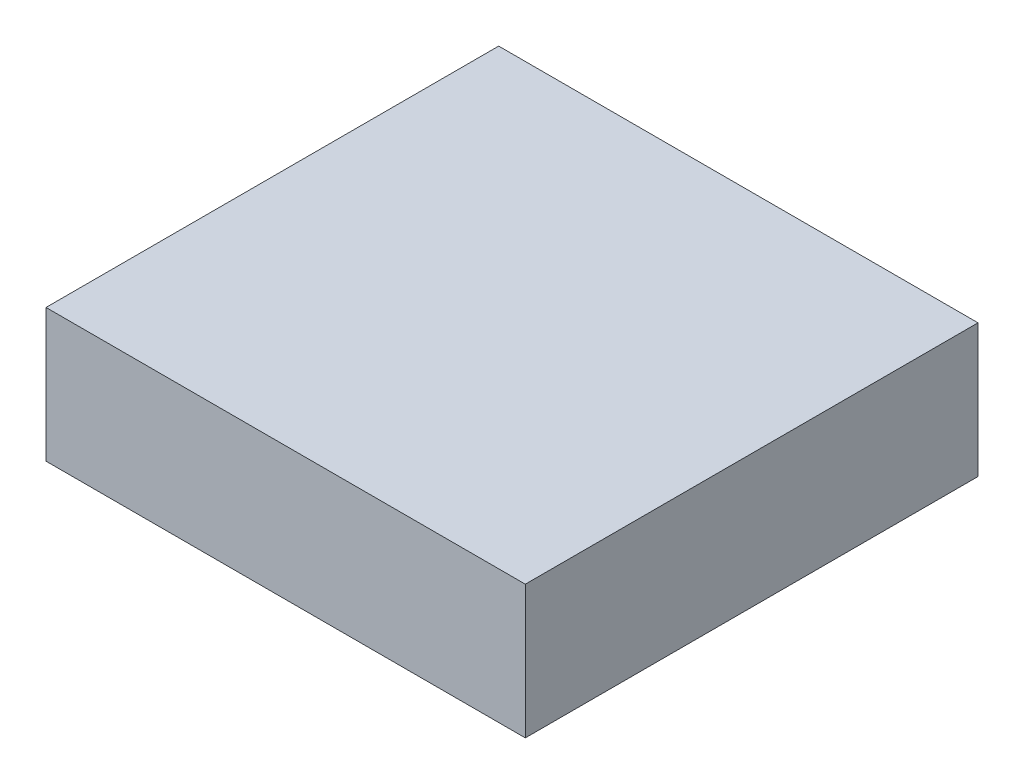
SolidWorks part; units mm, degrees
material "Aço 4140"
ref_plane "Plano frontal" through (0, 0, 0) normal (0, 0, 1) x (1, 0, 0)
ref_plane "Plano superior" through (0, 0, 0) normal (0, 1, 0) x (1, 0, 0)
ref_plane "Plano direito" through (0, 0, 0) normal (1, 0, 0) x (0, 0, -1)
sketch "Esboço1" plane through (0, 0, 0) normal (1, 0, 0) x (0, 0, -1)
  line L1 (-42.5, -12.5) -> (42.5, -12.5)
  line L2 (-42.5, -12.5) -> (-42.5, 12.5)
  line L3 (-42.5, 12.5) -> (42.5, 12.5)
  line L4 (42.5, -12.5) -> (42.5, 12.5)
  line L5 (-42.5, -12.5) -> (42.5, 12.5) construction
  line L6 (-42.5, 12.5) -> (42.5, -12.5) construction
  point P0 (0, 0)
  dimension "D1" = 85
  dimension "D2" = 25
extrude "Ressalto-extrusão1" add sketch "Esboço1" along normal blind 90
